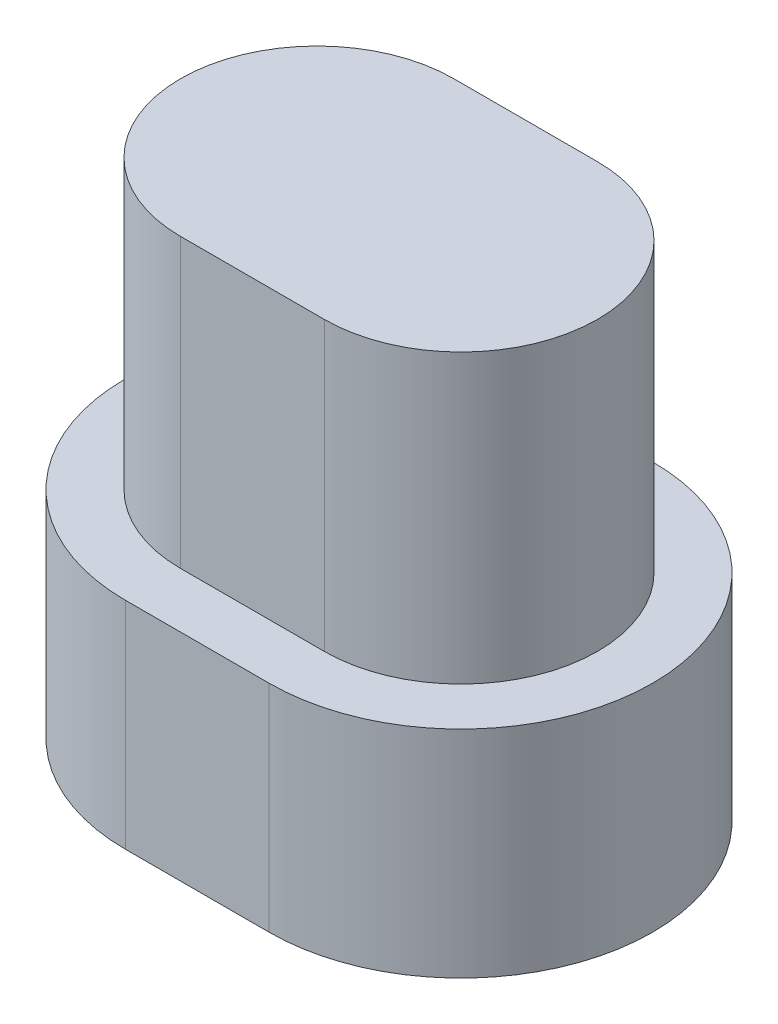
SolidWorks part; units mm, degrees
ref_plane "前视基准面" through (0, 0, 0) normal (0, 0, 1) x (1, 0, 0)
ref_plane "上视基准面" through (0, 0, 0) normal (0, 1, 0) x (1, 0, 0)
ref_plane "右视基准面" through (0, 0, 0) normal (1, 0, 0) x (0, 0, -1)
other "Configuration Table"
sketch "草图1" plane through (0, 0, 0) normal (0, 1, 0) x (1, 0, 0)
  line L0 (0, 0) -> (3, 0) construction
  line L1 (0, 2.85) -> (3, 2.85)
  line L2 (0, -2.85) -> (3, -2.85)
  arc A0 (0, 2.85) -> (0, -2.85) centre (0, 0) ccw
  arc A1 (3, -2.85) -> (3, 2.85) centre (3, 0) ccw
  point P3 (1.5, 0)
  dimension "D2" = 2.85
  dimension "D1" = 3
extrude "凸台-拉伸1" add sketch "草图1" along normal blind 6
sketch "草图2" plane through (0, 0, 0) normal (0, -1, 0) x (1, 0, 0)
  line L0 (0, 0) -> (3, 0) construction
  line L1 (0, 4) -> (3, 4)
  line L2 (0, -4) -> (3, -4)
  arc A0 (0, 4) -> (0, -4) centre (0, 0) ccw
  arc A1 (3, -4) -> (3, 4) centre (3, 0) ccw
  arc A2 (3, -2.85) -> (3, 2.85) centre (3, 0) ccw construction
  arc A3 (0, 2.85) -> (0, -2.85) centre (0, 0) ccw construction
  point P3 (1.5, 0)
  dimension "D1" = 4
extrude "凸台-拉伸2" add sketch "草图2" along normal blind 4.5
